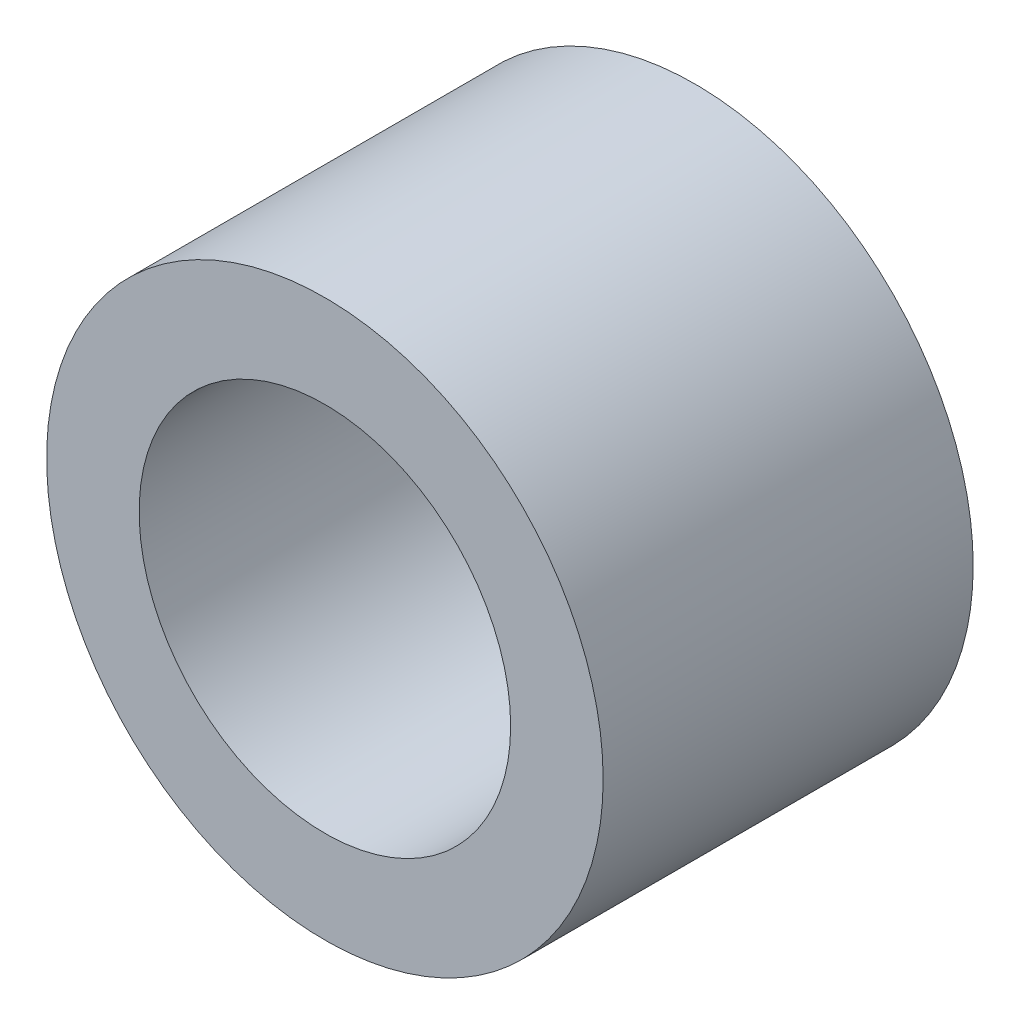
SolidWorks part; units mm, degrees
ref_plane "Front Plane" through (0, 0, 0) normal (0, 0, 1) x (1, 0, 0)
ref_plane "Top Plane" through (0, 0, 0) normal (0, 1, 0) x (1, 0, 0)
ref_plane "Right Plane" through (0, 0, 0) normal (1, 0, 0) x (0, 0, -1)
sketch "Sketch1" plane through (0, 0, 0) normal (0, 0, 1) x (1, 0, 0)
  circle A0 centre (0, 0) radius 4.7752
  circle A1 centre (0, 0) radius 3.1877
  dimension "D1" = 9.5504
  dimension "ID" = 6.3754
extrude "Extrude1" add sketch "Sketch1" along normal mid plane 6.35
sketch "Sketch2" plane through (0, 0, 0) normal (1, 0, 0) x (0, 0, -1)
  line L0 (-3.175, -3.1877) -> (3.175, -3.1877) construction
  line L3 (3.175, 3.1877) -> (-3.175, 3.1877) construction
  line L5 (-3.175, -3.1877) -> (3.175, -3.1877)
  line L6 (3.175, 3.1877) -> (-3.175, 3.1877)
sketch "Sketch4" plane through (0, 0, 3.175) normal (0, 0, 1) x (1, 0, 0)
  line L0 (0, 0) -> (-2.254, 2.254)
  line L1 (0, -6.1258) -> (0, 6.1258) construction
  circle A0 centre (0, 0) radius 3.1877 construction
  dimension "D1" = 45
